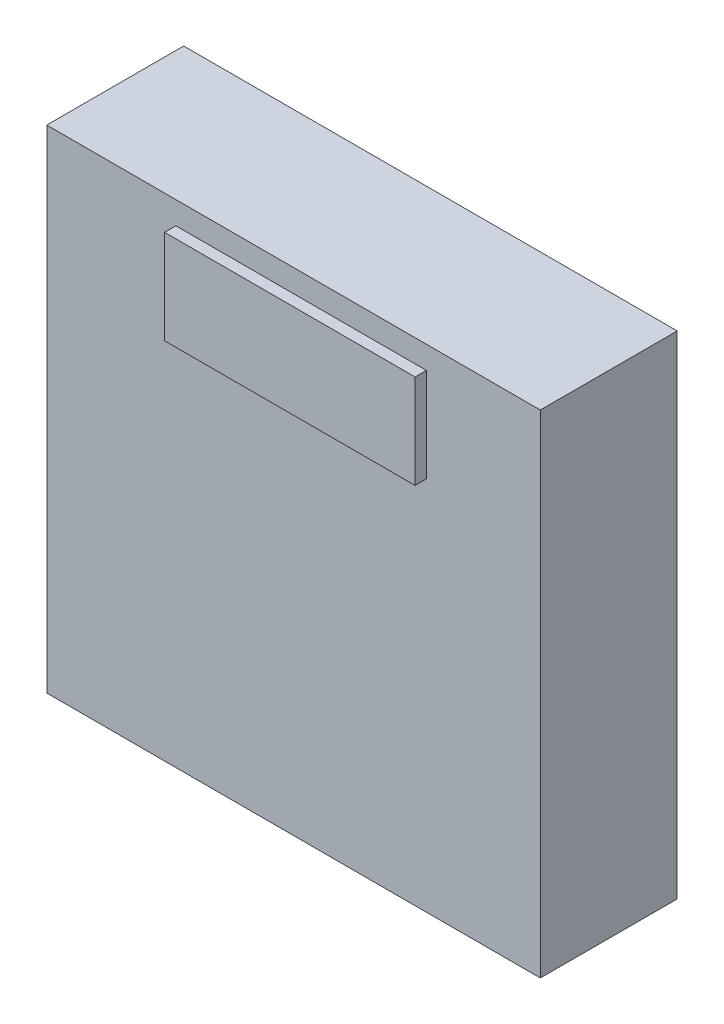
SolidWorks part; units mm, degrees
ref_plane "Front Plane" through (0, 0, 0) normal (0, 0, 1) x (1, 0, 0)
ref_plane "Top Plane" through (0, 0, 0) normal (0, 1, 0) x (1, 0, 0)
ref_plane "Right Plane" through (0, 0, 0) normal (1, 0, 0) x (0, 0, -1)
sketch "Sketch1" plane through (0, 0, 0) normal (0, 0, 1) x (1, 0, 0)
  line L1 (55.2958, -55.1117) -> (-55.2958, -55.1117)
  line L2 (55.2958, -55.1117) -> (55.2958, 55.1116)
  line L3 (55.2958, 55.1116) -> (-55.2958, 55.1116)
  line L4 (-55.2958, -55.1117) -> (-55.2958, 55.1116)
  line L5 (55.2958, -55.1117) -> (-55.2958, 55.1116) construction
  line L6 (55.2958, 55.1116) -> (-55.2958, -55.1117) construction
  point P0 (0, 0)
extrude "Boss-Extrude1" add sketch "Sketch1" along normal blind 30.6832
sketch "Sketch3" plane through (0, 0, 30.6832) normal (0, 0, 1) x (1, 0, 0)
  line L0 (-55.2958, 55.1116) -> (-55.2958, -55.1117) construction
  line L1 (-26.3652, 50.0316) -> (29.7688, 50.0316)
  line L2 (-26.3652, 50.0316) -> (-26.3652, 28.9877)
  line L3 (-26.3652, 28.9877) -> (29.7688, 28.9877)
  line L4 (29.7688, 50.0316) -> (29.7688, 28.9877)
  line L5 (55.2958, 55.1116) -> (-55.2958, 55.1116) construction
  dimension "D1" = 28.9306
  dimension "D2" = 5.08
extrude "Boss-Extrude2" add sketch "Sketch3" along normal blind 2.54
